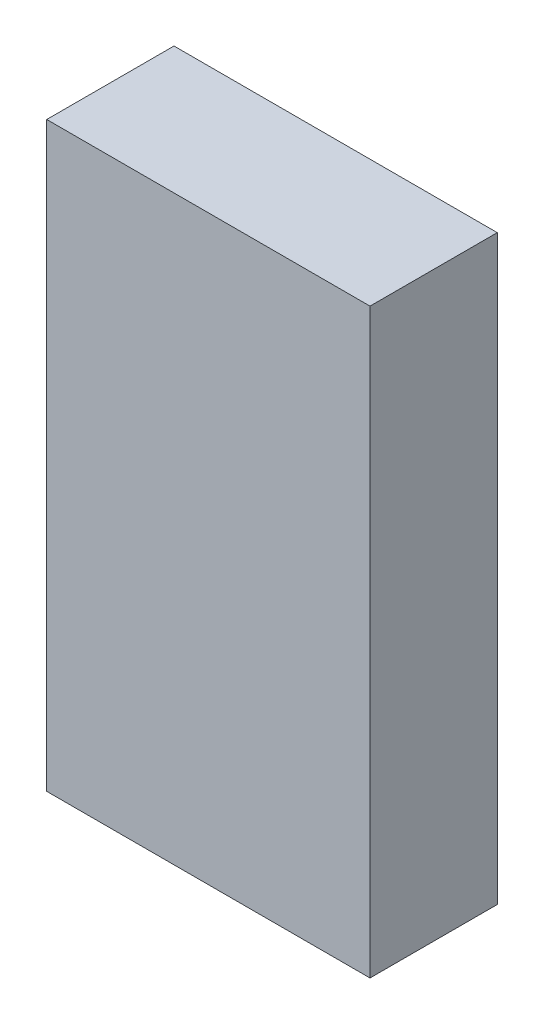
SolidWorks part; units mm, degrees
ref_plane "Front Plane" through (0, 0, 0) normal (0, 0, 1) x (1, 0, 0)
ref_plane "Top Plane" through (0, 0, 0) normal (0, 1, 0) x (1, 0, 0)
ref_plane "Right Plane" through (0, 0, 0) normal (1, 0, 0) x (0, 0, -1)
sketch "Sketch1" plane through (0, 0, 0) normal (0, 0, 1) x (1, 0, 0)
  line L0 (-1.27, 2.286) -> (1.27, 2.286)
  line L1 (1.27, 2.286) -> (1.27, -2.286)
  line L2 (1.27, -2.286) -> (-1.27, -2.286)
  line L3 (-1.27, -2.286) -> (-1.27, 2.286)
extrude "Component_Outline" add sketch "Sketch1" along normal blind 1 separate body
sketch3d "3DSketch1"
  line L0 (0, 0, 0) -> (1, 0, 0)
  line L1 (0, 0, 0) -> (0, 1, 0)
  line L2 (0, 0, 0) -> (0, 0, 1)
  point P0 (0, 0, 0)
